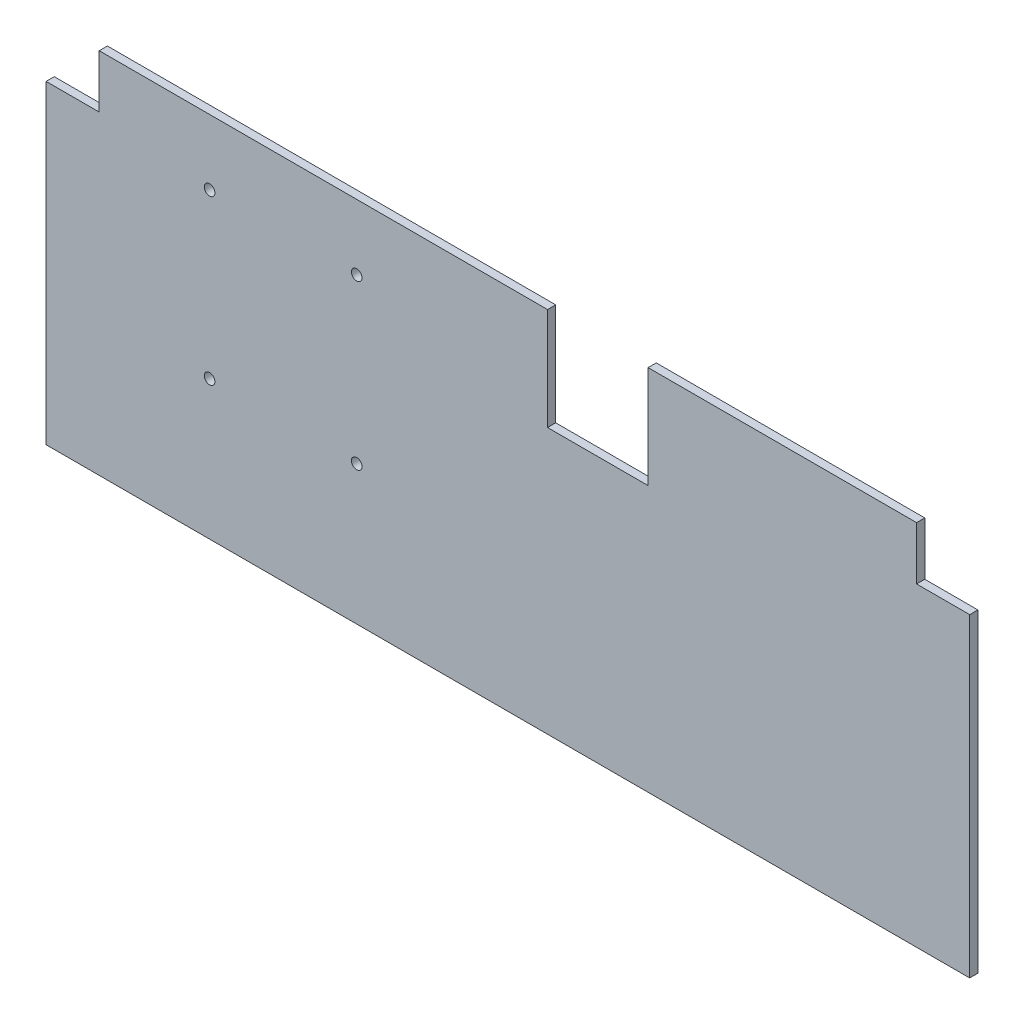
SolidWorks part; units mm, degrees
ref_plane "Front Plane" through (0, 0, 0) normal (0, 0, 1) x (1, 0, 0)
ref_plane "Top Plane" through (0, 0, 0) normal (0, 1, 0) x (1, 0, 0)
ref_plane "Right Plane" through (0, 0, 0) normal (1, 0, 0) x (0, 0, -1)
sketch "Sketch1" plane through (0, 0, 0) normal (0, 0, 1) x (1, 0, 0)
  line L0 (0, 300.7391) -> (0, -350.58) construction
  line L1 (-565, 200) -> (565, 200)
  line L2 (-565, 200) -> (-565, -250)
  line L3 (-565, -250) -> (565, -250)
  line L4 (565, 200) -> (565, -250)
  dimension "D1" = 450
  dimension "D2" = 1130
  dimension "D3" = 200
extrude "Boss-Extrude1" add sketch "Sketch1" along normal blind 10
sketch "Sketch2" plane through (0, 0, 10) normal (0, 0, 1) x (1, 0, 0)
  line L1 (-565, 200) -> (-500, 200)
  line L2 (-565, 200) -> (-565, 135)
  line L3 (-565, 135) -> (-500, 135)
  line L4 (-500, 200) -> (-500, 135)
  dimension "D1" = 65
  dimension "D2" = 65
extrude "Cut-Extrude1" cut sketch "Sketch2" against normal through all
mirror "Mirror1" about plane through (0, 0, 0) normal (1, 0, 0) of "Cut-Extrude1"
sketch "Sketch3" plane through (0, 0, 10) normal (0, 0, 1) x (1, 0, 0)
  line L0 (500, 200) -> (-500, 200) construction
  line L1 (48.5, 200) -> (171.5, 200)
  line L2 (48.5, 200) -> (48.5, 75)
  line L3 (48.5, 75) -> (171.5, 75)
  line L4 (171.5, 200) -> (171.5, 75)
  line L5 (110, 200) -> (110, 17.4188) construction
  line L6 (565, -250) -> (565, 135) construction
  dimension "D1" = 125
  dimension "D2" = 123
  dimension "D3" = 455
extrude "Cut-Extrude2" cut sketch "Sketch3" against normal through all
sketch "Sketch4" plane through (0, 0, 10) normal (0, 0, 1) x (1, 0, 0)
  line L0 (-590.0197, 20) -> (25.526, 20) construction
  line L1 (-275, 232.3733) -> (-275, -344.5389) construction
  line L2 (48.5, 75) -> (171.5, 75) construction
  line L3 (110, 75) -> (110, 317.1046) construction
  point P0 (-365, 120)
  point P1 (-365, -80)
  point P2 (-185, -80)
  point P3 (-185, 120)
  point P8 (0, 0)
  point P9 (0, 0)
  dimension "D1" = 180
  dimension "D2" = 200
  dimension "D3" = 55
  dimension "D4" = 295
hole_wizard "Ø13.0 (13) Diameter Hole1" positions "Sketch5" profile "Sketch6" hole size "Ø13.0" standard "ISO" end condition through all
sketch "Sketch5" plane through (0, 0, 10) normal (0, 0, 1) x (1, 0, 0)
  point P0 (-365, 120)
  point P3 (-185, 120)
  point P6 (-185, -80)
  point P9 (-365, -80)
sketch "Sketch6" plane through (-365, 120, 10) normal (1, 0, 0) x (0, -1, 0)
  line L0 (0, 0) -> (0, 10)
  line L1 (0, 10) -> (6.5, 10)
  line L2 (6.5, 10) -> (6.5, 0)
  line L5 (6.5, 0) -> (0, 0)
  line L11 (0, -6.35) -> (0, 107.95) construction
  dimension "Thru Hole Dia." = 13
  dimension "Thru Hole Depth" = 10
